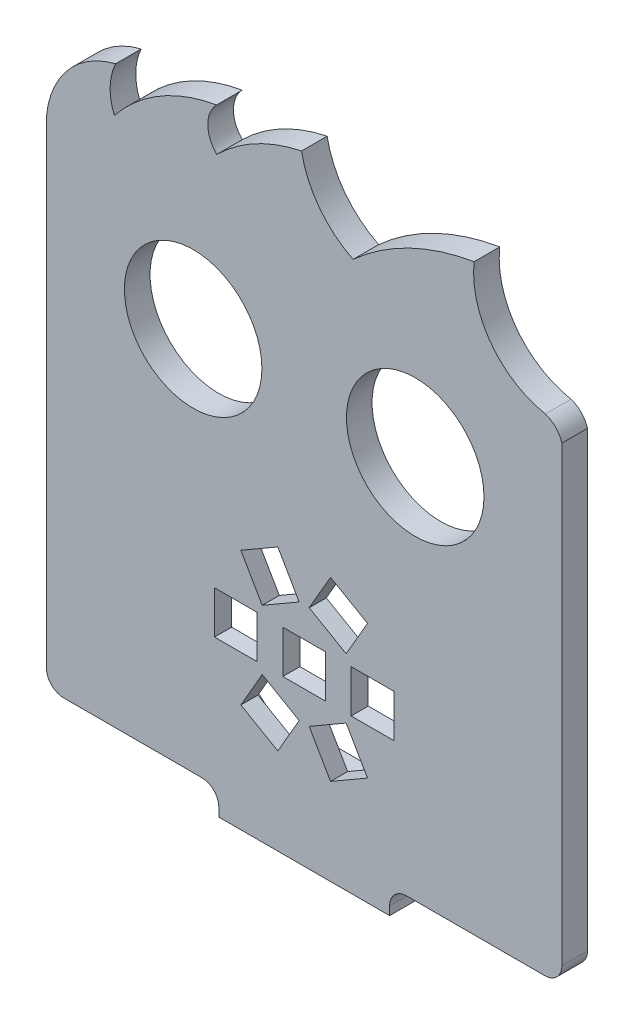
SolidWorks part; units mm, degrees
ref_plane "Alzado" through (0, 0, 0) normal (0, 0, 1) x (1, 0, 0)
ref_plane "Planta" through (0, 0, 0) normal (0, 1, 0) x (1, 0, 0)
ref_plane "Vista lateral" through (0, 0, 0) normal (1, 0, 0) x (0, 0, -1)
sketch "Model" plane through (0, 0, 0) normal (0, 0, 1) x (1, 0, 0)
  line L0 (53.2839, -43.3643) -> (57.614, -45.8643)
  line L1 (57.614, -45.8643) -> (60.114, -41.5341)
  line L2 (60.114, -41.5341) -> (55.7839, -39.0341)
  line L3 (55.7839, -39.0341) -> (53.2839, -43.3643)
  line L4 (63.7839, -45.8643) -> (68.114, -43.3643)
  line L5 (68.114, -43.3643) -> (65.614, -39.0341)
  line L6 (65.614, -39.0341) -> (61.2839, -41.5341)
  line L7 (61.2839, -41.5341) -> (63.7839, -45.8643)
  line L8 (71.199, -38.021) -> (71.199, -33.021)
  line L9 (71.199, -33.021) -> (66.199, -33.021)
  line L10 (66.199, -33.021) -> (66.199, -38.021)
  line L11 (66.199, -38.021) -> (71.199, -38.021)
  line L12 (68.114, -27.6777) -> (63.7839, -25.1777)
  line L13 (63.7839, -25.1777) -> (61.2839, -29.5079)
  line L14 (61.2839, -29.5079) -> (65.614, -32.0079)
  line L15 (65.614, -32.0079) -> (68.114, -27.6777)
  line L16 (57.614, -25.1777) -> (53.2839, -27.6777)
  line L17 (53.2839, -27.6777) -> (55.7839, -32.0079)
  line L18 (55.7839, -32.0079) -> (60.114, -29.5079)
  line L19 (60.114, -29.5079) -> (57.614, -25.1777)
  line L20 (50.199, -33.021) -> (50.199, -38.021)
  line L21 (50.199, -38.021) -> (55.199, -38.021)
  line L22 (55.199, -38.021) -> (55.199, -33.021)
  line L23 (55.199, -33.021) -> (50.199, -33.021)
  line L24 (58.199, -33.021) -> (58.199, -38.021)
  line L25 (58.199, -38.021) -> (63.199, -38.021)
  line L26 (63.199, -38.021) -> (63.199, -33.021)
  line L27 (63.199, -33.021) -> (58.199, -33.021)
  line L28 (50.699, -56.021) -> (70.699, -56.021)
  line L29 (60.699, -33.021) -> (60.699, -56.021) construction
  line L30 (63.199, -35.521) -> (58.199, -35.521) construction
  line L74 (50.699, -55.021) -> (50.699, -56.021)
  line L75 (48.699, -53.021) -> (32.5271, -53.021)
  line L76 (30.5271, 4.9744) -> (30.5271, -51.021)
  line L77 (90.8708, -51.021) -> (90.8708, 1.979)
  line L78 (88.8708, -53.021) -> (72.699, -53.021)
  line L79 (70.699, -56.021) -> (70.699, -55.021)
  circle A0 centre (47.699, -8.021) radius 8.05
  circle A1 centre (73.699, -8.021) radius 8.05
  arc A2 (50.699, -55.021) -> (48.699, -53.021) centre (48.699, -55.021) ccw
  arc A3 (70.699, -55.021) -> (72.699, -53.021) centre (72.699, -55.021) cw
  arc A31 (30.5271, -51.021) -> (32.5271, -53.021) centre (32.5271, -51.021) ccw
  arc A32 (38.6183, 14.3189) -> (30.5271, 4.9744) centre (41.1247, 3.9735) ccw
  arc A33 (38.6183, 14.3189) -> (38.4712, 8.9961) centre (44.4932, 11.4932) ccw
  arc A34 (50.4388, 16.0514) -> (38.4712, 8.9961) centre (53.6269, -3.0341) ccw
  arc A35 (50.4388, 16.0514) -> (50.4619, 11.0514) centre (52.9503, 13.5629) ccw
  arc A36 (60.3874, 16.3614) -> (50.4619, 11.0514) centre (64.38, -3.0332) ccw
  arc A37 (60.3874, 16.3614) -> (66.4243, 8.3891) centre (71.3781, 18.4121) ccw
  arc A38 (80.5924, 15.2365) -> (66.4243, 8.3891) centre (85.17, -12.3168) ccw
  arc A39 (80.5924, 15.2365) -> (88.9405, 3.9735) centre (90.8379, 14.1051) ccw
  arc A40 (90.8708, 1.979) -> (88.9405, 3.9735) centre (87.9945, 1.1265) ccw
  arc A41 (88.8708, -53.021) -> (90.8708, -51.021) centre (88.8708, -51.021) ccw
  dimension "D1" = 2
  dimension "D2" = 17.5
extrude "Saliente-Extruir1" add sketch "Model" along normal blind 3
sketch "Croquis3" plane through (0, 0, 0) normal (0, 0, -1) x (-1, 0, 0)
  line L0 (-70.699, -56.021) -> (-70.699, -53.021)
  line L1 (-70.699, -53.021) -> (-50.699, -53.021)
  line L2 (-50.699, -53.021) -> (-50.699, -56.021)
  line L3 (-50.699, -56.021) -> (-70.699, -56.021)
  dimension "D1" = 3
extrude "Saliente-Extruir2" add sketch "Croquis3" along normal blind 8
sketch "Croquis4" plane through (0, -53.021, 0) normal (0, 1, 0) x (1, 0, 0)
  line L0 (60.699, 8) -> (60.699, 0) construction
  line L1 (50.699, 8) -> (70.699, 8) construction
  line L2 (50.699, 0) -> (70.699, 0) construction
  circle A0 centre (66.699, 3.5) radius 1.5
  circle A1 centre (54.699, 3.5) radius 1.5
  dimension "D1" = 3.5
  dimension "D2" = 6
extrude "Cortar-Extruir1" cut sketch "Croquis4" against normal blind 3
sketch "Croquis5" plane through (0, -53.021, 0) normal (0, 1, 0) x (1, 0, 0)
  circle A0 centre (66.699, 3.5) radius 2.25
  circle A1 centre (54.699, 3.5) radius 2.25
extrude "Cortar-Extruir2" cut sketch "Croquis5" against normal blind 1
fillet "Redondeo1" radius 2 2 edges at (50.699, -54.521, -8) (70.699, -54.521, -8)
sketch "Croquis6" plane through (0, 0, 0) normal (0, 0, -1) x (-1, 0, 0)
  line L0 (-90.8708, -35.521) -> (-30.5271, -35.521) construction
  line L1 (-90.8708, -51.021) -> (-90.8708, 1.979) construction
  line L2 (-30.5271, 4.9744) -> (-30.5271, -51.021) construction
  line L3 (-32.5271, -53.021) -> (-48.699, -53.021) construction
  circle A0 centre (-60.699, -35.521) radius 12
  dimension "D1" = 17.5
extrude "Cortar-Extruir3" cut sketch "Croquis6" against normal blind 1
